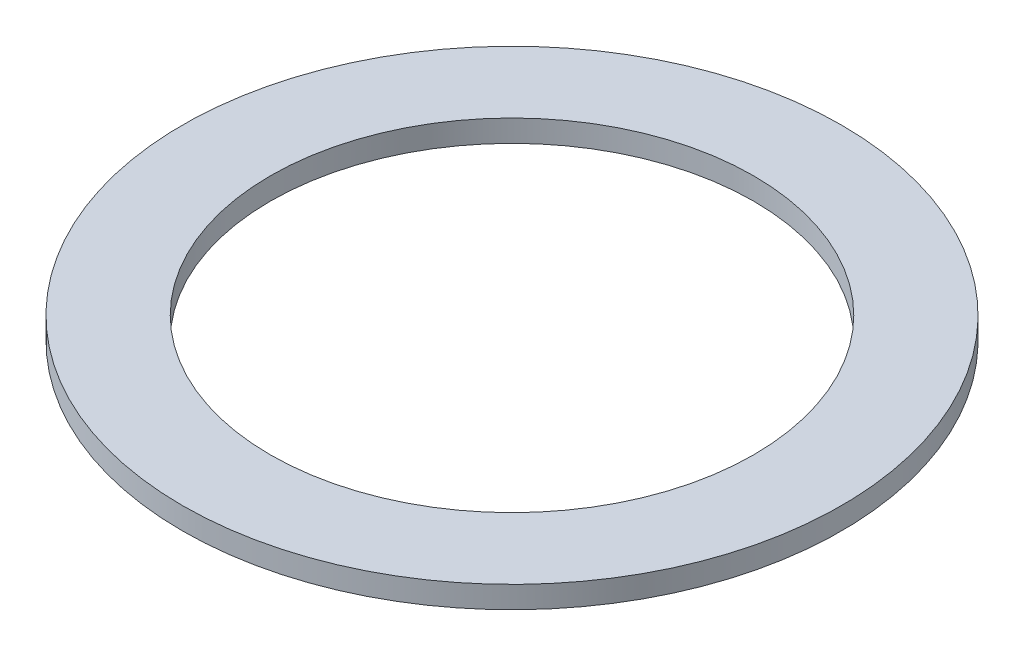
SolidWorks part; units mm, degrees
ref_plane "Front Plane" through (0, 0, 0) normal (0, 0, 1) x (1, 0, 0)
ref_plane "Top Plane" through (0, 0, 0) normal (0, 1, 0) x (1, 0, 0)
ref_plane "Right Plane" through (0, 0, 0) normal (1, 0, 0) x (0, 0, -1)
sketch "Sketch1" [suppressed] plane through (0, 0, 0) normal (0, 1, 0) x (1, 0, 0)
  line L0 (64.8373, 172.8232) -> (110.5573, 172.8232)
  line L1 (-226.3291, 17.3244) -> (-175.5291, 17.3244)
  line L2 (-226.3291, 17.3244) -> (-226.3291, -28.3956)
  line L3 (-226.3291, -28.3956) -> (-175.5291, -28.3956)
  line L4 (-175.5291, 17.3244) -> (-175.5291, -28.3956)
  line L5 (-25.8367, 73.6932) -> (-25.9918, 109.2529) construction
  line L6 (-25.8367, 73.6932) -> (-25.6815, 109.2529) construction
  line L7 (-25.9918, 104.9349) -> (-25.9918, 109.2529)
  line L8 (-25.6815, 109.2529) -> (-25.7004, 104.9349)
  line L9 (64.8373, 172.8232) -> (64.8373, 127.1032)
  line L10 (64.8373, 127.1032) -> (110.5573, 127.1032)
  line L11 (110.5573, 172.8232) -> (110.5573, 127.1032)
  line L12 (-157.7491, 17.3244) -> (-157.7491, -28.3956)
  line L13 (-157.7491, -28.3956) -> (-106.9491, -28.3956)
  line L14 (-106.9491, 17.3244) -> (-106.9491, -28.3956)
  line L15 (-157.7491, 17.3244) -> (-106.9491, 17.3244)
  line L16 (-89.1691, 17.3244) -> (-89.1691, -28.3956)
  line L17 (-89.1691, -28.3956) -> (-38.3691, -28.3956)
  line L18 (-38.3691, 17.3244) -> (-38.3691, -28.3956)
  line L19 (-89.1691, 17.3244) -> (-38.3691, 17.3244)
  line L20 (-20.5891, 17.3244) -> (-20.5891, -28.3956)
  line L21 (-20.5891, -28.3956) -> (30.2109, -28.3956)
  line L22 (30.2109, 17.3244) -> (30.2109, -28.3956)
  line L23 (-20.5891, 17.3244) -> (30.2109, 17.3244)
  line L24 (-1.1346, 99.273) -> (-4.1342, 96.1669)
  line L25 (-9.1423, 105.0909) -> (-11.1694, 101.2783)
  line L26 (-7.5988, 99.0594) -> (-5.0608, 102.5528)
  line L27 (-4.8097, 102.3704) -> (-7.363, 98.8882)
  line L28 (9.1831, 79.8682) -> (4.9307, 79.1184)
  line L29 (6.1244, 89.2817) -> (2.2434, 87.3888)
  line L30 (3.8279, 83.495) -> (7.9346, 84.8293)
  line L31 (8.0305, 84.5342) -> (3.9181, 83.2178)
  line L32 (6.1244, 58.1048) -> (2.2434, 59.9976)
  line L33 (9.1831, 67.5183) -> (4.9307, 68.2681)
  line L34 (3.9238, 64.1866) -> (8.0305, 62.8523)
  line L35 (7.9346, 62.5571) -> (3.8338, 63.9094)
  line L36 (-9.1423, 42.2956) -> (-11.1694, 46.1082)
  line L37 (-1.1346, 48.1135) -> (-4.1342, 51.2196)
  line L38 (-7.3478, 48.5094) -> (-4.8097, 45.0161)
  line L39 (-5.0608, 44.8337) -> (-7.5835, 48.338)
  line L40 (-30.7857, 38.4793) -> (-30.1847, 42.7553)
  line L41 (-20.8877, 38.4793) -> (-21.4886, 42.7553)
  line L42 (-25.6815, 42.4516) -> (-25.6815, 38.1336)
  line L43 (-25.9918, 38.1336) -> (-25.973, 42.4515)
  line L44 (-50.5387, 48.1135) -> (-47.5392, 51.2196)
  line L45 (-42.5311, 42.2956) -> (-40.5039, 46.1082)
  line L46 (-44.0745, 48.327) -> (-46.6126, 44.8337)
  line L47 (-46.8636, 45.0161) -> (-44.3104, 48.4983)
  line L48 (-60.8564, 67.5183) -> (-56.604, 68.2681)
  line L49 (-57.7978, 58.1048) -> (-53.9168, 59.9976)
  line L50 (-55.5013, 63.8915) -> (-59.608, 62.5571)
  line L51 (-59.7039, 62.8523) -> (-55.5914, 64.1687)
  line L52 (-57.7978, 89.2817) -> (-53.9168, 87.3888)
  line L53 (-60.8564, 79.8682) -> (-56.604, 79.1184)
  line L54 (-55.5972, 83.1999) -> (-59.7039, 84.5342)
  line L55 (-59.608, 84.8293) -> (-55.5072, 83.4771)
  line L56 (-42.5311, 105.0909) -> (-40.5039, 101.2783)
  line L57 (-50.5387, 99.273) -> (-47.5392, 96.1669)
  line L58 (-44.3256, 98.877) -> (-46.8636, 102.3704)
  line L59 (-46.6126, 102.5528) -> (-44.0898, 99.0484)
  line L180 (-25.8367, 73.6932) -> (-20.8877, 108.9072) construction
  line L181 (-25.8367, 73.6932) -> (-30.7857, 108.9072) construction
  line L182 (-30.7857, 108.9072) -> (-30.1847, 104.6312)
  line L183 (-20.8877, 108.9072) -> (-21.4886, 104.6312)
  line L211 (-126.2276, 73.4215) -> (-126.2276, 95.0115) construction
  line L212 (-126.2276, 73.4215) -> (-107.5301, 62.6265) construction
  line L213 (-126.2276, 73.4215) -> (-144.9251, 62.6265) construction
  line L214 (-126.2276, 73.4215) -> (-124.1129, 88.4686) construction
  line L215 (-124.1129, 88.4686) -> (-124.4737, 85.9012)
  line L216 (-126.2276, 73.4215) -> (-112.139, 67.7293) construction
  line L217 (-112.139, 67.7293) -> (-114.5429, 68.7005)
  line L218 (-126.2276, 73.4215) -> (-120.633, 92.0012) construction
  line L219 (-120.633, 92.0012) -> (-121.2529, 89.9423) construction
  line L220 (-119.4187, 91.6355) -> (-120.0387, 89.5767)
  line L221 (-121.8472, 92.3668) -> (-122.4672, 90.3079)
  line L222 (-116.2075, 90.0378) -> (-117.3179, 88.1965) construction
  line L223 (-115.1216, 89.3829) -> (-116.2319, 87.5416)
  line L224 (-117.2934, 90.6926) -> (-118.4038, 88.8513)
  line L225 (-112.4058, 87.04) -> (-113.9375, 85.5309) construction
  line L226 (-111.5158, 86.1367) -> (-113.0474, 84.6276)
  line L227 (-113.2958, 87.9433) -> (-114.8275, 86.4342)
  line L228 (-109.4646, 83.1943) -> (-111.3222, 82.1113) construction
  line L229 (-108.826, 82.0988) -> (-110.6835, 81.0158)
  line L230 (-110.1033, 84.2898) -> (-111.9609, 83.2068)
  line L231 (-107.5671, 78.7402) -> (-109.6349, 78.1508) construction
  line L232 (-107.2195, 77.5207) -> (-109.2873, 76.9313)
  line L233 (-107.9147, 79.9597) -> (-109.9825, 79.3703)
  line L234 (-106.8312, 73.955) -> (-108.9806, 73.8959) construction
  line L235 (-106.7963, 72.6874) -> (-108.9457, 72.6283)
  line L236 (-106.8661, 75.2226) -> (-109.0155, 75.1635)
  line L237 (-107.3029, 69.1366) -> (-109.4, 69.6114) construction
  line L238 (-107.5829, 67.8998) -> (-109.68, 68.3746)
  line L239 (-107.0229, 70.3734) -> (-109.12, 70.8482)
  line L240 (-138.2014, 64.0665) -> (-136.1584, 65.6627)
  line L241 (-114.2537, 64.0665) -> (-116.2968, 65.6627)
  line L242 (-112.9344, 59.2866) -> (-114.4075, 60.8529) construction
  line L243 (-113.8582, 58.4178) -> (-115.3312, 59.9842)
  line L244 (-112.0107, 60.1553) -> (-113.4837, 61.7217)
  line L245 (-116.8475, 56.4357) -> (-117.8869, 58.3179) construction
  line L246 (-117.9576, 55.8227) -> (-118.997, 57.7049)
  line L247 (-115.7374, 57.0487) -> (-116.7768, 58.9309)
  line L248 (-121.3445, 54.6422) -> (-121.8856, 56.7232) construction
  line L249 (-122.5718, 54.3231) -> (-123.1129, 56.4041)
  line L250 (-120.1172, 54.9614) -> (-120.6583, 57.0424)
  line L251 (-126.1456, 54.0179) -> (-126.1547, 56.1681) construction
  line L252 (-127.4136, 54.0126) -> (-127.4227, 56.1627)
  line L253 (-124.8775, 54.0233) -> (-124.8866, 56.1735)
  line L254 (-130.9517, 54.6016) -> (-130.4282, 56.6871) construction
  line L255 (-132.1816, 54.9104) -> (-131.6582, 56.9959)
  line L256 (-129.7218, 54.2929) -> (-129.1983, 56.3784)
  line L257 (-135.4637, 56.357) -> (-134.4403, 58.2479) construction
  line L258 (-136.579, 56.9606) -> (-135.5555, 58.8516)
  line L259 (-134.3485, 55.7534) -> (-133.325, 57.6443)
  line L260 (-139.4008, 59.1747) -> (-137.941, 60.7534) construction
  line L261 (-140.3319, 60.0356) -> (-138.8721, 61.6143)
  line L262 (-138.4697, 58.3138) -> (-137.0099, 59.8925)
  line L263 (-128.3423, 88.4686) -> (-127.9815, 85.9012)
  line L264 (-140.3162, 67.7293) -> (-137.9123, 68.7005)
  line L265 (-145.1154, 68.9767) -> (-143.0224, 69.4692) construction
  line L266 (-145.4058, 70.2111) -> (-143.3128, 70.7036)
  line L267 (-144.8249, 67.7423) -> (-142.7319, 68.2349)
  line L268 (-145.6278, 73.791) -> (-143.478, 73.75) construction
  line L269 (-145.6036, 75.0588) -> (-143.4538, 75.0179)
  line L270 (-145.6519, 72.5231) -> (-143.5021, 72.4822)
  line L271 (-144.9324, 78.5822) -> (-142.8597, 78.0104) construction
  line L272 (-144.5951, 79.8047) -> (-142.5224, 79.2328)
  line L273 (-145.2697, 77.3598) -> (-143.197, 76.7879)
  line L274 (-143.0726, 83.0522) -> (-141.2059, 81.985) construction
  line L275 (-142.4432, 84.1531) -> (-140.5765, 83.0859)
  line L276 (-143.702, 81.9513) -> (-141.8353, 80.8841)
  line L277 (-140.164, 86.9226) -> (-138.6197, 85.4265) construction
  line L278 (-139.2817, 87.8334) -> (-137.7373, 86.3373)
  line L279 (-141.0463, 86.0118) -> (-139.502, 84.5157)
  line L280 (-136.3878, 89.9525) -> (-135.2619, 88.1206) construction
  line L281 (-135.3075, 90.6165) -> (-134.1816, 88.7846)
  line L282 (-137.4682, 89.2885) -> (-136.3423, 87.4566)
  line L283 (-131.9791, 91.9532) -> (-131.3417, 89.8996) construction
  line L284 (-130.768, 92.3291) -> (-130.1306, 90.2755)
  line L285 (-133.1902, 91.5773) -> (-132.5528, 89.5238)
  line L286 (-205.9574, 96.8125) -> (-207.4037, 91.4149)
  line L287 (-214.6337, 97.9548) -> (-212.0937, 97.9548)
  line L288 (-214.6337, 97.9548) -> (-214.6337, 92.3668)
  line L289 (-214.6337, 92.3668) -> (-212.0937, 92.3668)
  line L290 (-212.0937, 97.9548) -> (-212.0937, 92.3668)
  line L291 (-208.4109, 97.4699) -> (-205.9574, 96.8125)
  line L292 (-208.4109, 97.4699) -> (-209.8571, 92.0723)
  line L293 (-209.8571, 92.0723) -> (-207.4037, 91.4149)
  line L294 (-200.3258, 94.121) -> (-203.1198, 89.2817)
  line L295 (-202.5255, 95.391) -> (-200.3258, 94.121)
  line L296 (-202.5255, 95.391) -> (-205.3195, 90.5517)
  line L297 (-205.3195, 90.5517) -> (-203.1198, 89.2817)
  line L298 (-195.5828, 90.0636) -> (-199.5341, 86.1123)
  line L299 (-197.3788, 91.8597) -> (-195.5828, 90.0636)
  line L300 (-197.3788, 91.8597) -> (-201.3301, 87.9084)
  line L301 (-201.3301, 87.9084) -> (-199.5341, 86.1123)
  line L302 (-192.0515, 84.9169) -> (-196.8908, 82.1229)
  line L303 (-193.3215, 87.1166) -> (-192.0515, 84.9169)
  line L304 (-193.3215, 87.1166) -> (-198.1608, 84.3226)
  line L305 (-198.1608, 84.3226) -> (-196.8908, 82.1229)
  line L306 (-189.9725, 79.0316) -> (-195.3701, 77.5853)
  line L307 (-190.6299, 81.4851) -> (-189.9725, 79.0316)
  line L308 (-190.6299, 81.4851) -> (-196.0275, 80.0388)
  line L309 (-196.0275, 80.0388) -> (-195.3701, 77.5853)
  line L310 (-189.4877, 72.8088) -> (-195.0757, 72.8088)
  line L311 (-189.4877, 75.3488) -> (-189.4877, 72.8088)
  line L312 (-189.4877, 75.3488) -> (-195.0757, 75.3488)
  line L313 (-195.0757, 75.3488) -> (-195.0757, 72.8088)
  line L314 (-190.6299, 66.6725) -> (-196.0275, 68.1188)
  line L315 (-189.9725, 69.1259) -> (-190.6299, 66.6725)
  line L316 (-189.9725, 69.1259) -> (-195.3701, 70.5722)
  line L317 (-195.3701, 70.5722) -> (-196.0275, 68.1188)
  line L318 (-193.3215, 61.0409) -> (-198.1608, 63.8349)
  line L319 (-192.0515, 63.2406) -> (-193.3215, 61.0409)
  line L320 (-192.0515, 63.2406) -> (-196.8908, 66.0346)
  line L321 (-196.8908, 66.0346) -> (-198.1608, 63.8349)
  line L322 (-197.3788, 56.2979) -> (-201.3301, 60.2492)
  line L323 (-195.5828, 58.0939) -> (-197.3788, 56.2979)
  line L324 (-195.5828, 58.0939) -> (-199.5341, 62.0452)
  line L325 (-199.5341, 62.0452) -> (-201.3301, 60.2492)
  line L326 (-202.5255, 52.7666) -> (-205.3195, 57.6059)
  line L327 (-200.3258, 54.0366) -> (-202.5255, 52.7666)
  line L328 (-200.3258, 54.0366) -> (-203.1198, 58.8759)
  line L329 (-203.1198, 58.8759) -> (-205.3195, 57.6059)
  line L330 (-208.4109, 50.6876) -> (-209.8571, 56.0852)
  line L331 (-205.9574, 51.345) -> (-208.4109, 50.6876)
  line L332 (-205.9574, 51.345) -> (-207.4037, 56.7426)
  line L333 (-207.4037, 56.7426) -> (-209.8571, 56.0852)
  line L334 (-214.6337, 50.2028) -> (-214.6337, 55.7908)
  line L335 (-212.0937, 50.2028) -> (-214.6337, 50.2028)
  line L336 (-212.0937, 50.2028) -> (-212.0937, 55.7908)
  line L337 (-212.0937, 55.7908) -> (-214.6337, 55.7908)
  line L338 (-220.77, 51.345) -> (-219.3237, 56.7426)
  line L339 (-218.3165, 50.6876) -> (-220.77, 51.345)
  line L340 (-218.3165, 50.6876) -> (-216.8702, 56.0852)
  line L341 (-216.8702, 56.0852) -> (-219.3237, 56.7426)
  line L342 (-226.4015, 54.0366) -> (-223.6075, 58.8759)
  line L343 (-224.2018, 52.7666) -> (-226.4015, 54.0366)
  line L344 (-224.2018, 52.7666) -> (-221.4078, 57.6059)
  line L345 (-221.4078, 57.6059) -> (-223.6075, 58.8759)
  line L346 (-231.1446, 58.0939) -> (-227.1933, 62.0452)
  line L347 (-229.3485, 56.2979) -> (-231.1446, 58.0939)
  line L348 (-229.3485, 56.2979) -> (-225.3972, 60.2492)
  line L349 (-225.3972, 60.2492) -> (-227.1933, 62.0452)
  line L350 (-234.6759, 63.2406) -> (-229.8366, 66.0346)
  line L351 (-233.4059, 61.0409) -> (-234.6759, 63.2406)
  line L352 (-233.4059, 61.0409) -> (-228.5666, 63.8349)
  line L353 (-228.5666, 63.8349) -> (-229.8366, 66.0346)
  line L354 (-236.7548, 69.1259) -> (-231.3572, 70.5722)
  line L355 (-236.0974, 66.6725) -> (-236.7548, 69.1259)
  line L356 (-236.0974, 66.6725) -> (-230.6998, 68.1188)
  line L357 (-230.6998, 68.1188) -> (-231.3572, 70.5722)
  line L358 (-237.2397, 75.3488) -> (-231.6517, 75.3488)
  line L359 (-237.2397, 72.8088) -> (-237.2397, 75.3488)
  line L360 (-237.2397, 72.8088) -> (-231.6517, 72.8088)
  line L361 (-231.6517, 72.8088) -> (-231.6517, 75.3488)
  line L362 (-236.0974, 81.4851) -> (-230.6998, 80.0388)
  line L363 (-236.7548, 79.0316) -> (-236.0974, 81.4851)
  line L364 (-236.7548, 79.0316) -> (-231.3572, 77.5853)
  line L365 (-231.3572, 77.5853) -> (-230.6998, 80.0388)
  line L366 (-233.4059, 87.1166) -> (-228.5666, 84.3226)
  line L367 (-234.6759, 84.9169) -> (-233.4059, 87.1166)
  line L368 (-234.6759, 84.9169) -> (-229.8366, 82.1229)
  line L369 (-229.8366, 82.1229) -> (-228.5666, 84.3226)
  line L370 (-229.3485, 91.8597) -> (-225.3972, 87.9084)
  line L371 (-231.1446, 90.0636) -> (-229.3485, 91.8597)
  line L372 (-231.1446, 90.0636) -> (-227.1933, 86.1123)
  line L373 (-227.1933, 86.1123) -> (-225.3972, 87.9084)
  line L374 (-224.2018, 95.391) -> (-221.4078, 90.5517)
  line L375 (-226.4015, 94.121) -> (-224.2018, 95.391)
  line L376 (-226.4015, 94.121) -> (-223.6075, 89.2817)
  line L377 (-223.6075, 89.2817) -> (-221.4078, 90.5517)
  line L378 (-218.3165, 97.4699) -> (-216.8702, 92.0723)
  line L379 (-220.77, 96.8125) -> (-218.3165, 97.4699)
  line L380 (-220.77, 96.8125) -> (-219.3237, 91.4149)
  line L381 (-219.3237, 91.4149) -> (-216.8702, 92.0723)
  circle A0 centre (-126.8346, 73.6932) radius 38.1
  circle A1 centre (-25.8367, 73.6932) radius 38.1
  circle A2 centre (64.0045, 73.6932) radius 38.1
  arc A3 (-25.7004, 104.9349) -> (-21.4886, 104.6312) centre (-25.8367, 73.6932) cw
  arc A4 (-30.1847, 104.6312) -> (-25.9918, 104.9349) centre (-25.8367, 73.6932) cw
  arc A5 (-30.7857, 108.9072) -> (-25.9918, 109.2529) centre (-25.8367, 73.6932) cw
  circle A6 centre (-126.8346, 73.6932) radius 27.94
  arc A7 (-4.8097, 102.3704) -> (-1.1346, 99.273) centre (-25.8367, 73.6932) cw
  arc A8 (-9.1423, 105.0909) -> (-5.0608, 102.5528) centre (-25.8367, 73.6932) cw
  circle A9 centre (64.0045, 73.6932) radius 35.56
  arc A10 (-25.6815, 109.2529) -> (-20.8877, 108.9072) centre (-25.8367, 73.6932) cw
  arc A11 (-7.363, 98.8882) -> (-4.1342, 96.1669) centre (-25.8367, 73.6932) cw
  arc A12 (-11.1694, 101.2783) -> (-7.5988, 99.0594) centre (-25.8367, 73.6932) cw
  arc A13 (8.0305, 84.5342) -> (9.1831, 79.8682) centre (-25.8367, 73.6932) cw
  arc A14 (6.1244, 89.2817) -> (7.9346, 84.8293) centre (-25.8367, 73.6932) cw
  arc A15 (3.9181, 83.2178) -> (4.9307, 79.1184) centre (-25.8367, 73.6932) cw
  arc A16 (2.2434, 87.3888) -> (3.8279, 83.495) centre (-25.8367, 73.6932) cw
  arc A17 (7.9346, 62.5571) -> (6.1244, 58.1048) centre (-25.8367, 73.6932) cw
  arc A18 (9.1831, 67.5183) -> (8.0305, 62.8523) centre (-25.8367, 73.6932) cw
  arc A19 (3.8338, 63.9094) -> (2.2434, 59.9976) centre (-25.8367, 73.6932) cw
  arc A20 (4.9307, 68.2681) -> (3.9238, 64.1866) centre (-25.8367, 73.6932) cw
  arc A21 (-5.0608, 44.8337) -> (-9.1423, 42.2956) centre (-25.8367, 73.6932) cw
  arc A22 (-1.1346, 48.1135) -> (-4.8097, 45.0161) centre (-25.8367, 73.6932) cw
  arc A23 (-7.5835, 48.338) -> (-11.1694, 46.1082) centre (-25.8367, 73.6932) cw
  arc A24 (-4.1342, 51.2196) -> (-7.3478, 48.5094) centre (-25.8367, 73.6932) cw
  arc A25 (-25.9918, 38.1336) -> (-30.7857, 38.4793) centre (-25.8367, 73.6932) cw
  arc A26 (-20.8877, 38.4793) -> (-25.6815, 38.1336) centre (-25.8367, 73.6932) cw
  arc A27 (-25.973, 42.4515) -> (-30.1847, 42.7553) centre (-25.8367, 73.6932) cw
  arc A28 (-21.4886, 42.7553) -> (-25.6815, 42.4516) centre (-25.8367, 73.6932) cw
  arc A29 (-46.8636, 45.0161) -> (-50.5387, 48.1135) centre (-25.8367, 73.6932) cw
  arc A30 (-42.5311, 42.2956) -> (-46.6126, 44.8337) centre (-25.8367, 73.6932) cw
  arc A31 (-44.3104, 48.4983) -> (-47.5392, 51.2196) centre (-25.8367, 73.6932) cw
  arc A32 (-40.5039, 46.1082) -> (-44.0745, 48.327) centre (-25.8367, 73.6932) cw
  arc A33 (-59.7039, 62.8523) -> (-60.8564, 67.5183) centre (-25.8367, 73.6932) cw
  arc A34 (-57.7978, 58.1048) -> (-59.608, 62.5571) centre (-25.8367, 73.6932) cw
  arc A35 (-55.5914, 64.1687) -> (-56.604, 68.2681) centre (-25.8367, 73.6932) cw
  arc A36 (-53.9168, 59.9976) -> (-55.5013, 63.8915) centre (-25.8367, 73.6932) cw
  arc A37 (-59.608, 84.8293) -> (-57.7978, 89.2817) centre (-25.8367, 73.6932) cw
  arc A38 (-60.8564, 79.8682) -> (-59.7039, 84.5342) centre (-25.8367, 73.6932) cw
  arc A39 (-55.5072, 83.4771) -> (-53.9168, 87.3888) centre (-25.8367, 73.6932) cw
  arc A40 (-56.604, 79.1184) -> (-55.5972, 83.1999) centre (-25.8367, 73.6932) cw
  arc A41 (-46.6126, 102.5528) -> (-42.5311, 105.0909) centre (-25.8367, 73.6932) cw
  arc A42 (-50.5387, 99.273) -> (-46.8636, 102.3704) centre (-25.8367, 73.6932) cw
  arc A43 (-44.0898, 99.0484) -> (-40.5039, 101.2783) centre (-25.8367, 73.6932) cw
  arc A44 (-47.5392, 96.1669) -> (-44.3256, 98.877) centre (-25.8367, 73.6932) cw
  circle A86 centre (-213.3637, 74.0788) radius 38.1
  circle A87 centre (-213.3637, 74.0788) radius 27.94
  circle A88 centre (-169.4932, 146.3194) radius 38.1
  circle A89 centre (-169.4932, 146.3194) radius 27.94
  circle A90 centre (-84.2528, 146.1615) radius 38.1
  circle A91 centre (-84.2528, 146.1615) radius 27.94
  circle A92 centre (18.3555, 145.2989) radius 38.1
  circle A93 centre (-126.2276, 73.4215) radius 21.59
  circle A94 centre (-126.2276, 73.4215) radius 11.43
  arc A95 (-124.4737, 85.9012) -> (-114.5429, 68.7005) centre (-126.2276, 73.4215) cw
  arc A96 (-112.139, 67.7293) -> (-124.1129, 88.4686) centre (-126.2276, 73.4215) ccw
  arc A97 (-119.4187, 91.6355) -> (-121.8472, 92.3668) centre (-120.633, 92.0012) ccw
  arc A98 (-122.4672, 90.3079) -> (-120.0387, 89.5767) centre (-121.2529, 89.9423) ccw
  arc A99 (-115.1216, 89.3829) -> (-117.2934, 90.6926) centre (-116.2075, 90.0378) ccw
  arc A100 (-118.4038, 88.8513) -> (-116.2319, 87.5416) centre (-117.3179, 88.1965) ccw
  arc A101 (-111.5158, 86.1367) -> (-113.2958, 87.9433) centre (-112.4058, 87.04) ccw
  arc A102 (-114.8275, 86.4342) -> (-113.0474, 84.6276) centre (-113.9375, 85.5309) ccw
  arc A103 (-108.826, 82.0988) -> (-110.1033, 84.2898) centre (-109.4646, 83.1943) ccw
  arc A104 (-111.9609, 83.2068) -> (-110.6835, 81.0158) centre (-111.3222, 82.1113) ccw
  arc A105 (-107.2195, 77.5207) -> (-107.9147, 79.9597) centre (-107.5671, 78.7402) ccw
  arc A106 (-109.9825, 79.3703) -> (-109.2873, 76.9313) centre (-109.6349, 78.1508) ccw
  arc A107 (-106.7963, 72.6874) -> (-106.8661, 75.2226) centre (-106.8312, 73.955) ccw
  arc A108 (-109.0155, 75.1635) -> (-108.9457, 72.6283) centre (-108.9806, 73.8959) ccw
  arc A109 (-107.5829, 67.8998) -> (-107.0229, 70.3734) centre (-107.3029, 69.1366) ccw
  arc A110 (-109.12, 70.8482) -> (-109.68, 68.3746) centre (-109.4, 69.6114) ccw
  circle A111 centre (-126.2276, 92.0012) radius 1.2173
  circle A112 centre (-110.1371, 64.1316) radius 1.2173
  arc A113 (-138.2014, 64.0665) -> (-114.2537, 64.0665) centre (-126.2276, 73.4215) ccw
  arc A114 (-116.2968, 65.6627) -> (-136.1584, 65.6627) centre (-126.2276, 73.4215) cw
  arc A115 (-113.8582, 58.4178) -> (-112.0107, 60.1553) centre (-112.9344, 59.2866) ccw
  arc A116 (-113.4837, 61.7217) -> (-115.3312, 59.9842) centre (-114.4075, 60.8529) ccw
  arc A117 (-117.9576, 55.8227) -> (-115.7374, 57.0487) centre (-116.8475, 56.4357) ccw
  arc A118 (-116.7768, 58.9309) -> (-118.997, 57.7049) centre (-117.8869, 58.3179) ccw
  arc A119 (-122.5718, 54.3231) -> (-120.1172, 54.9614) centre (-121.3445, 54.6422) ccw
  arc A120 (-120.6583, 57.0424) -> (-123.1129, 56.4041) centre (-121.8856, 56.7232) ccw
  arc A121 (-127.4136, 54.0126) -> (-124.8775, 54.0233) centre (-126.1456, 54.0179) ccw
  arc A122 (-124.8866, 56.1735) -> (-127.4227, 56.1627) centre (-126.1547, 56.1681) ccw
  arc A123 (-132.1816, 54.9104) -> (-129.7218, 54.2929) centre (-130.9517, 54.6016) ccw
  arc A124 (-129.1983, 56.3784) -> (-131.6582, 56.9959) centre (-130.4282, 56.6871) ccw
  arc A125 (-136.579, 56.9606) -> (-134.3485, 55.7534) centre (-135.4637, 56.357) ccw
  arc A126 (-133.325, 57.6443) -> (-135.5555, 58.8516) centre (-134.4403, 58.2479) ccw
  arc A127 (-140.3319, 60.0356) -> (-138.4697, 58.3138) centre (-139.4008, 59.1747) ccw
  arc A128 (-137.0099, 59.8925) -> (-138.8721, 61.6143) centre (-137.941, 60.7534) ccw
  circle A129 centre (-142.3181, 64.1316) radius 1.2173
  arc A130 (-128.3423, 88.4686) -> (-140.3162, 67.7293) centre (-126.2276, 73.4215) ccw
  arc A131 (-137.9123, 68.7005) -> (-127.9815, 85.9012) centre (-126.2276, 73.4215) cw
  arc A132 (-145.4058, 70.2111) -> (-144.8249, 67.7423) centre (-145.1154, 68.9767) ccw
  arc A133 (-142.7319, 68.2349) -> (-143.3128, 70.7036) centre (-143.0224, 69.4692) ccw
  arc A134 (-145.6036, 75.0588) -> (-145.6519, 72.5231) centre (-145.6278, 73.791) ccw
  arc A135 (-143.5021, 72.4822) -> (-143.4538, 75.0179) centre (-143.478, 73.75) ccw
  arc A136 (-144.5951, 79.8047) -> (-145.2697, 77.3598) centre (-144.9324, 78.5822) ccw
  arc A137 (-143.197, 76.7879) -> (-142.5224, 79.2328) centre (-142.8597, 78.0104) ccw
  arc A138 (-142.4432, 84.1531) -> (-143.702, 81.9513) centre (-143.0726, 83.0522) ccw
  arc A139 (-141.8353, 80.8841) -> (-140.5765, 83.0859) centre (-141.2059, 81.985) ccw
  arc A140 (-139.2817, 87.8334) -> (-141.0463, 86.0118) centre (-140.164, 86.9226) ccw
  arc A141 (-139.502, 84.5157) -> (-137.7373, 86.3373) centre (-138.6197, 85.4265) ccw
  arc A142 (-135.3075, 90.6165) -> (-137.4682, 89.2885) centre (-136.3878, 89.9525) ccw
  arc A143 (-136.3423, 87.4566) -> (-134.1816, 88.7846) centre (-135.2619, 88.1206) ccw
  arc A144 (-130.768, 92.3291) -> (-133.1902, 91.5773) centre (-131.9791, 91.9532) ccw
  arc A145 (-132.5528, 89.5238) -> (-130.1306, 90.2755) centre (-131.3417, 89.8996) ccw
  circle A146 centre (-213.3637, 74.0788) radius 25.4
  circle A147 centre (-213.3637, 74.0788) radius 17.018
  point P109 (-25.8367, 73.6932)
  point P378 (-25.8367, 73.6932)
  point P396 (-120.943, 90.9717)
  point P397 (-116.7627, 89.1171)
  point P414 (-113.1716, 86.2854)
  point P421 (-110.3934, 82.6528)
  point P428 (-108.601, 78.4455)
  point P435 (-107.9059, 73.9254)
  point P442 (-108.3515, 69.374)
  point P449 (-126.2276, 73.4215)
  point P452 (-113.6709, 60.0697)
  point P453 (-117.3672, 57.3768)
  point P470 (-121.6151, 55.6827)
  point P477 (-126.1501, 55.093)
  point P484 (-130.69, 55.6444)
  point P491 (-134.952, 57.3025)
  point P498 (-138.6709, 59.9641)
  point P507 (-144.0689, 69.223)
  point P508 (-144.5529, 73.7705)
  point P525 (-143.896, 78.2963)
  point P532 (-142.1392, 82.5186)
  point P539 (-139.3918, 86.1746)
  point P546 (-135.8249, 89.0366)
  point P553 (-131.6604, 90.9264)
  point P560 (-126.2276, 73.4215)
  point P661 (-213.3637, 74.0788)
  dimension "D1" = 76.2
  dimension "D2" = 76.2
  dimension "D3" = 76.2
  dimension "D5" = 45.72
  dimension "D6" = 4
  dimension "D11" = 55.88
  dimension "D14" = 71.12
  dimension "D15" = 45.72
  dimension "D27" = 76.2
  dimension "D28" = 55.88
  dimension "D29" = 76.2
  dimension "D30" = 55.88
  dimension "D31" = 76.2
  dimension "D32" = 55.88
  dimension "D40" = 50.8
  dimension "D41" = 34.036
  dimension "D7" = 50.8
  dimension "D8" = 45.72
  dimension "D9" = 24
  dimension "D10" = 0.5
  dimension "D33" = 120
  dimension "D34" = 120
  dimension "D35" = 8
  dimension "D36" = 8
  dimension "D37" = 17.2535
  dimension "D42" = 18.288
  dimension "D43" = 23.876
  dimension "D44" = 1.27
  dimension "D45" = 1.27
sketch "Sketch3" plane through (0, 0, 0) normal (0, 1, 0) x (1, 0, 0)
  circle A88 centre (-169.4932, 146.3194) radius 38.1
  circle A89 centre (-169.4932, 146.3194) radius 27.94
  dimension "D29" = 76.2
  dimension "D30" = 55.88
extrude "Boss-Extrude4" add sketch "Sketch3" along normal blind 2.54
